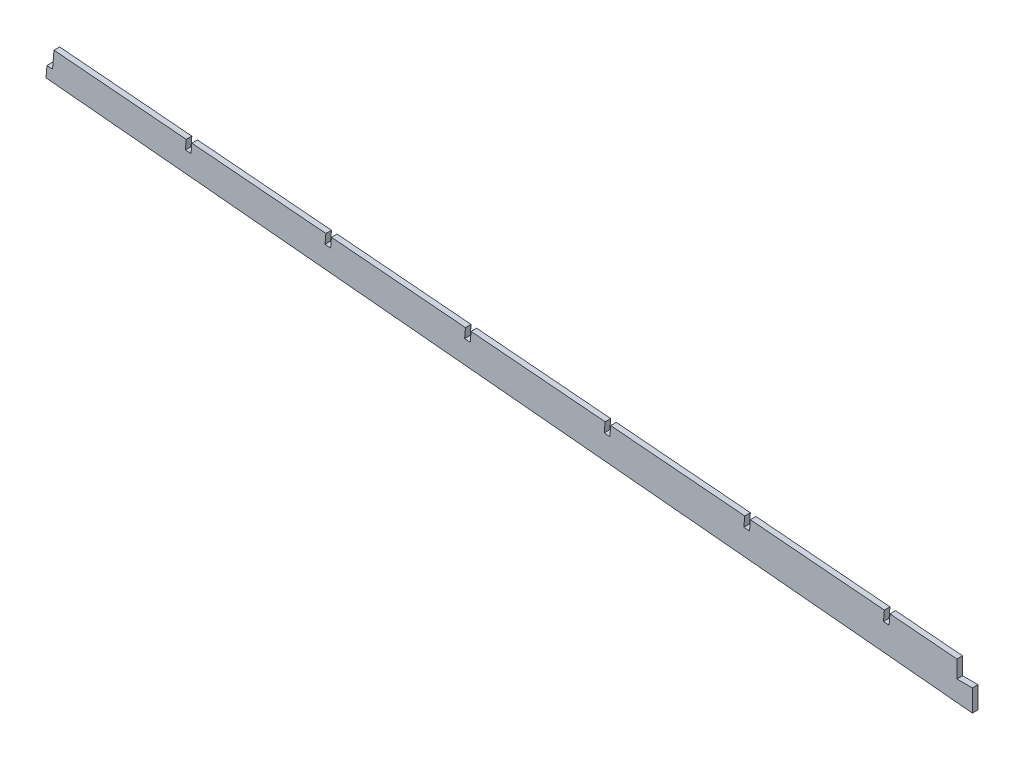
SolidWorks part; units mm, degrees
ref_plane "Front Plane" through (0, 0, 0) normal (0, 0, 1) x (1, 0, 0)
ref_plane "Top Plane" through (0, 0, 0) normal (0, 1, 0) x (1, 0, 0)
ref_plane "Right Plane" through (0, 0, 0) normal (1, 0, 0) x (0, 0, -1)
sketch "Sketch1" plane through (0, 0, 0) normal (0, 0, 1) x (1, 0, 0)
  line L0 (-951.0618, 63.2916) -> (-11.5367, -24.9026)
  line L8 (-8.3728, -25.1683) -> (-6.7788, -6.1851) construction
  line L9 (-6.7788, -6.1851) -> (-9.9426, -5.9194)
  line L10 (-9.9426, -5.9194) -> (-11.5367, -24.9026) construction
  line L11 (-11.5367, -24.9026) -> (-8.3728, -25.1683)
  line L12 (3.175, -25.5459) -> (3.175, -6.4959) construction
  line L13 (3.175, -6.4959) -> (0, -6.4959)
  line L14 (0, -6.4959) -> (0, -25.5459) construction
  line L15 (0, -25.5459) -> (3.175, -25.5459)
  line L17 (-943.9754, 109.7383) -> (-947.3666, 69.3536)
  line L19 (-8.3728, -25.1683) -> (0, -25.5459)
  line L20 (3.175, -25.5459) -> (152.4, -25.5459)
  line L21 (25.4, -0.1459) -> (69.85, -7.7659)
  line L22 (25.4, -0.1459) -> (-2.8123, -0.1459)
  line L23 (-2.8123, -0.1459) -> (-946.5481, 79.1019)
  line L24 (0, -6.4959) -> (0, -0.1459)
  line L25 (3.175, -6.4959) -> (3.175, -0.1459)
  line L26 (-6.7788, -6.1851) -> (-6.2474, 0.1426)
  line L27 (-9.9426, -5.9194) -> (-9.4113, 0.4083)
  line L28 (-9.9426, -5.9194) -> (-946.998, 73.7432)
  line L29 (69.85, -7.7659) -> (152.4, -7.7659)
  line L30 (152.4, -7.7659) -> (152.4, -25.5459)
  line L31 (76.2, -7.7659) -> (76.2, -25.5459)
  line L32 (79.375, -7.7659) -> (79.375, -25.5459)
  line L33 (76.2, -12.8459) -> (79.375, -12.8459)
  line L34 (15.875, -0.1459) -> (15.875, -5.2259)
  line L35 (15.875, -5.2259) -> (19.05, -5.2259)
  line L36 (19.05, -5.2259) -> (19.05, -0.1459)
  line L37 (92.075, -7.7659) -> (92.075, -12.8459)
  line L38 (92.075, -12.8459) -> (95.25, -12.8459)
  line L39 (95.25, -12.8459) -> (95.25, -7.7659)
  line L40 (136.525, -7.7659) -> (136.525, -12.8459)
  line L41 (136.525, -12.8459) -> (139.7, -12.8459)
  line L42 (139.7, -12.8459) -> (139.7, -7.7659)
  line L44 (-951.0618, 63.2916) -> (-950.5305, 69.6193)
  line L45 (-950.5305, 69.6193) -> (-947.3666, 69.3536)
  dimension "D1" = 25.4
  dimension "D2" = 6.35
extrude "Boss-Extrude1" add sketch "Sketch1" along normal blind 3.175
sketch "Sketch2" plane through (0, 0, 3.175) normal (0, 0, 1) x (1, 0, 0)
  line L1 (-73.9963, 64.5177) -> (-80.9723, -18.558)
  line L3 (-77.1601, 64.7834) -> (-84.1362, -18.2923)
  line L5 (-153.17, 68.7234) -> (-159.8855, -11.2491)
  line L7 (-232.3428, 72.9404) -> (-238.7996, -3.951)
  line L9 (-311.5203, 77.1018) -> (-317.7101, 3.3887)
  line L11 (-390.6978, 81.2631) -> (-396.6209, 10.7264)
  line L13 (-469.8812, 85.3537) -> (-475.5272, 18.1169)
  line L15 (-549.0652, 89.4374) -> (-554.4332, 25.5108)
  line L17 (-628.256, 93.4393) -> (-633.334, 32.9679)
  line L19 (-707.4489, 97.4177) -> (-712.2332, 40.4425)
  line L21 (-786.6506, 101.2897) -> (-791.1254, 48.0007)
  line L23 (-865.8569, 105.1088) -> (-870.014, 55.603)
  line L25 (-235.5067, 73.2061) -> (-241.9634, -3.6853)
  line L27 (-314.6841, 77.3675) -> (-320.874, 3.6544)
  line L29 (-393.8616, 81.5287) -> (-399.7848, 10.992)
  line L31 (-473.045, 85.6194) -> (-478.6911, 18.3826)
  line L33 (-552.229, 89.7031) -> (-557.5971, 25.7765)
  line L35 (-631.4199, 93.705) -> (-636.4978, 33.2336)
  line L37 (-710.6127, 97.6833) -> (-715.3971, 40.7082)
  line L39 (-789.8145, 101.5554) -> (-794.2893, 48.2664)
  line L41 (-9.9426, -5.9194) -> (-946.998, 73.7432)
  line L43 (-9.4113, 0.4083) -> (-946.5481, 79.1019)
  line L45 (-156.3339, 68.9891) -> (-163.0494, -10.9834)
  line L47 (-869.0207, 105.3745) -> (-873.1778, 55.8686)
  line M13 (-9.4113, 0.4083) -> (-946.5481, 79.1019)
extrude "Cut-Extrude1" cut sketch "Sketch2" against normal through all contours L47 L41 L23 M13 | L41 L21 L39 M13 | L41 L19 L37 M13 | L41 L17 L35 M13 | L41 L15 L33 M13 | L41 L13 L31 M13 | L41 L11 L29 M13 | L41 L9 L27 M13 | L41 L7 L25 M13 | L45 L41 L5 M13 | L41 L1 L3 M13
sketch "Sketch3" plane through (0, 0, 3.175) normal (0, 0, 1) x (1, 0, 0)
  line L0 (-435.837, 36.2162) -> (-435.837, 26.4516)
  line L1 (-397.9339, 33.0334) -> (-473.7401, 39.3991) construction
  line L2 (-435.837, 26.4516) -> (-427.1156, 26.4516)
  line L3 (-427.1156, 26.4516) -> (-427.1156, 14.1082)
  line L4 (-951.0618, 63.2916) -> (-11.5367, -24.9026) construction
  line L5 (-435.837, 36.2162) -> (191.1966, 26.4516)
  line L6 (191.1966, 26.4516) -> (150.839, -84.0542)
  line L7 (150.839, -84.0542) -> (-427.1156, 14.1082)
extrude "Cut-Extrude2" cut sketch "Sketch3" against normal blind 7.62 contours L7 L3 L2 L0 L5 L6
